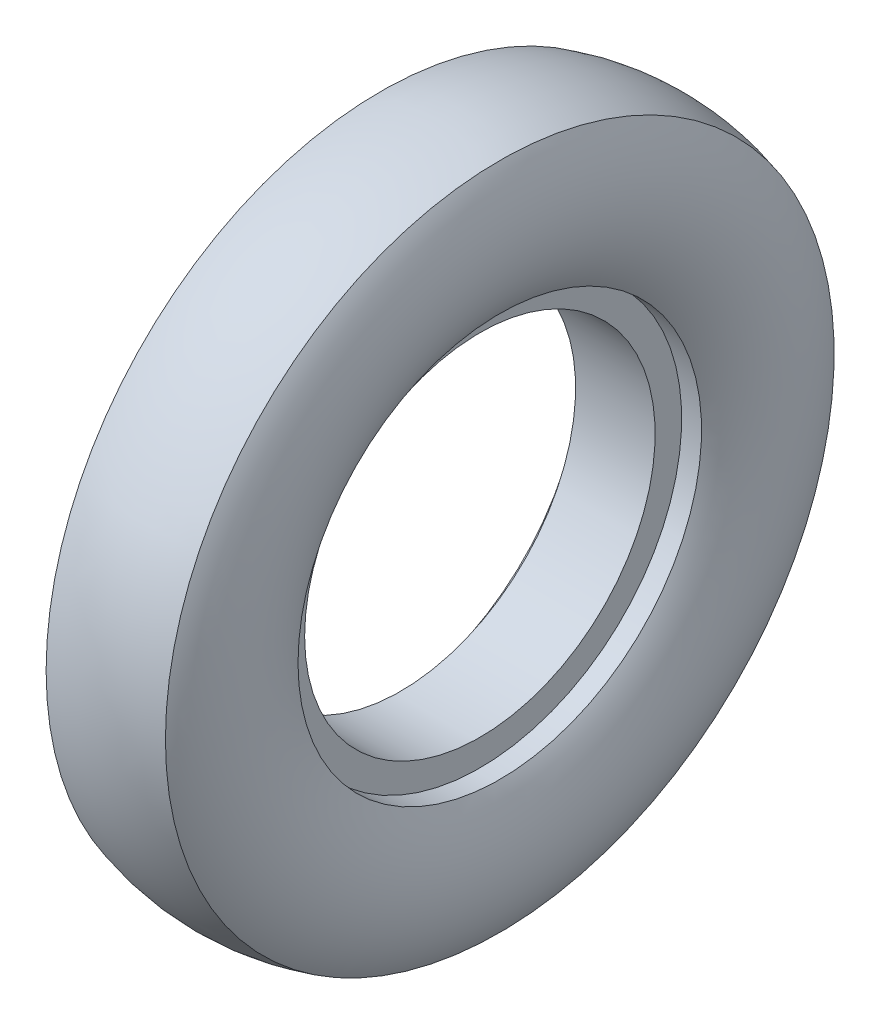
SolidWorks part; units mm, degrees
ref_plane "Front Plane" through (0, 0, 0) normal (0, 0, 1) x (1, 0, 0)
ref_plane "Top Plane" through (0, 0, 0) normal (0, 1, 0) x (1, 0, 0)
ref_plane "Right Plane" through (0, 0, 0) normal (1, 0, 0) x (0, 0, -1)
sketch "Sketch1" plane through (0, 0, 0) normal (0, 1, 0) x (1, 0, 0)
  line L0 (-18.9075, 0) -> (27.457, 0) construction
  line L2 (-0.9235, 13.2202) -> (5.0765, 13.2202)
  line L3 (-2.4235, 15.2202) -> (-2.4235, 25.2202) construction
  line L4 (5.4548, 15.2202) -> (5.4548, 14.2202) construction
  line L5 (6.5765, 15.2202) -> (5.0765, 15.2202)
  line L6 (5.0765, 15.2202) -> (5.0765, 13.2202)
  line L7 (-2.4235, 15.2202) -> (-0.9235, 15.2202)
  line L8 (-0.9235, 15.2202) -> (-0.9235, 13.2202)
  line L9 (6.5765, 15.2202) -> (6.5765, 25.2202) construction
  arc A3 (-2.4235, 25.2202) -> (-2.4235, 15.2202) centre (5.1598, 20.2202) ccw
  arc A4 (6.5765, 25.2202) -> (6.5765, 15.2202) centre (-1.0068, 20.2202) cw
  arc A5 (-2.4235, 25.2202) -> (6.5765, 25.2202) centre (2.0765, 10.303) cw
  point P8 (-3.9235, 20.2202)
  point P9 (-2.4235, 20.2202)
  point P11 (6.5765, 20.2202)
  point P12 (8.0765, 20.2202)
  point P20 (2.0765, 25.8841)
  dimension "D1" = 1.5
  dimension "D2" = 10
  dimension "D3" = 10
  dimension "D4" = 1.5
  dimension "D5" = 12
  dimension "D6" = 2
  dimension "D7" = 1.5
  dimension "D8" = 1.5
  dimension "D9" = 2
  dimension "D10" = 51.7683
revolve "Revolve1" add sketch "Sketch1" angle 360 about L0
